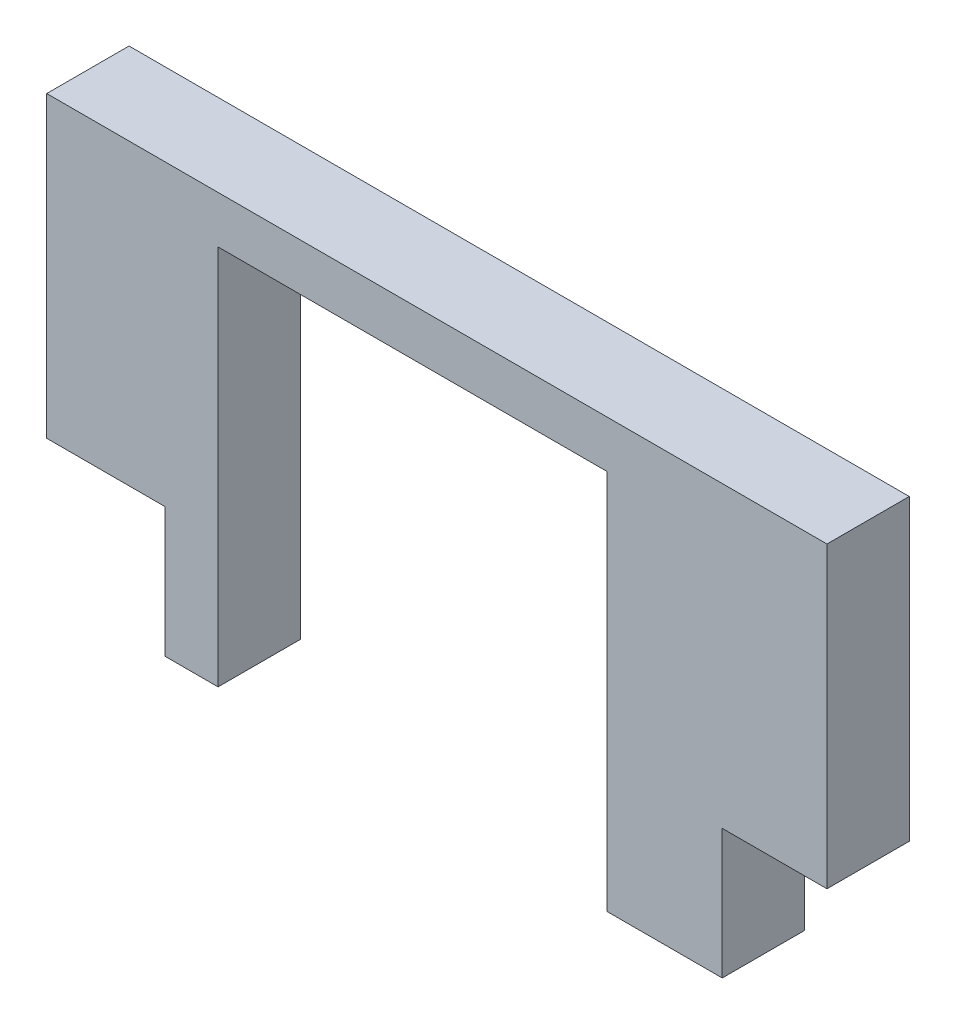
SolidWorks part; units mm, degrees
ref_plane "Front Plane" through (0, 0, 0) normal (0, 0, 1) x (1, 0, 0)
ref_plane "Top Plane" through (0, 0, 0) normal (0, 1, 0) x (1, 0, 0)
ref_plane "Right Plane" through (0, 0, 0) normal (1, 0, 0) x (0, 0, -1)
sketch "Sketch1" plane through (0, 0, 0) normal (0, 0, 1) x (1, 0, 0)
  line L0 (30.1, 0) -> (30.1, 16.66) construction
  line L1 (0, 16.66) -> (30.1, 16.66)
  line L2 (0, 16.66) -> (0, 6.34)
  line L4 (30.1, 16.66) -> (30.1, 6.34)
  line L5 (31.86, 6.34) -> (25.36, 6.34) construction
  line L6 (6.61, 6.34) -> (6.61, 14.84)
  line L7 (6.61, 14.84) -> (6.61, 0) construction
  line L8 (6.61, 14.84) -> (21.61, 14.84)
  line L9 (21.61, 0) -> (21.61, 14.84) construction
  line L10 (21.61, 14.84) -> (21.61, 6.34)
  line L11 (0, 6.34) -> (0, 5.14)
  line L13 (-2.14, 5.14) -> (2.86, 5.14) construction
  line L14 (0, 5.14) -> (4.56, 5.14)
  line L15 (6.61, 5.14) -> (6.61, 6.34)
  line L16 (30.1, 6.34) -> (30.1, 5.14)
  line L17 (30.36, 5.14) -> (26.06, 5.14) construction
  line L18 (30.1, 5.14) -> (26.06, 5.14)
  line L19 (21.61, 5.14) -> (21.61, 6.34)
  line L20 (4.56, 5.14) -> (4.56, 0.14)
  line L21 (4.56, 0.14) -> (6.61, 0.14)
  line L22 (6.61, -0.16) -> (6.61, 14.84) construction
  line L23 (6.61, 0.14) -> (6.61, 5.14)
  line L24 (21.61, 5.14) -> (21.61, 0.14)
  line L25 (21.61, 14.84) -> (21.61, -0.16) construction
  line L26 (21.61, 0.14) -> (25.36, 0.14)
  line L28 (26.06, 5.14) -> (26.06, 0.14)
  line L29 (26.06, 0.14) -> (25.36, 0.14)
extrude "Boss-Extrude1" add sketch "Sketch1" against normal blind 3.175
